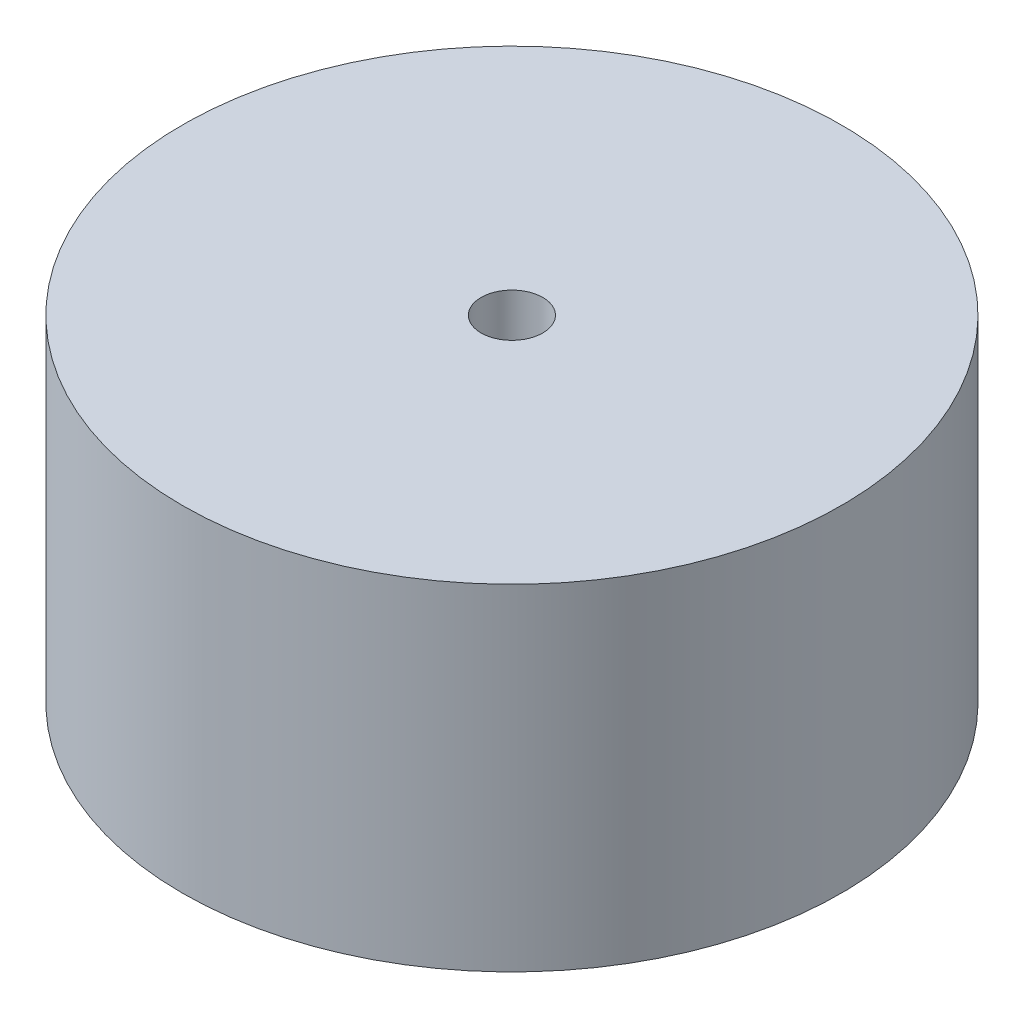
SolidWorks part; units mm, degrees
ref_plane "Front Plane" through (0, 0, 0) normal (0, 0, 1) x (1, 0, 0)
ref_plane "Top Plane" through (0, 0, 0) normal (0, 1, 0) x (1, 0, 0)
ref_plane "Right Plane" through (0, 0, 0) normal (1, 0, 0) x (0, 0, -1)
sketch "Sketch1" plane through (0, 0, 0) normal (0, 1, 0) x (1, 0, 0)
  circle A1 centre (0, 0) radius 17.375
extrude "Boss-Extrude1" add sketch "Sketch1" along normal blind 17.7
sketch "Sketch7" plane through (0, 0, 0) normal (0, -1, 0) x (1, 0, 0)
  circle A0 centre (0, 0) radius 13.545
extrude "Cut-Extrude4" cut sketch "Sketch7" against normal blind 8 contours A0
sketch "Sketch10" plane through (0, 8, 0) normal (0, -1, 0) x (1, 0, 0)
  circle A0 centre (0, 0) radius 3.485
extrude "Boss-Extrude3" add sketch "Sketch10" along normal blind 4 contours A0
sketch "Sketch11" plane through (0, 4, 0) normal (0, -1, 0) x (1, 0, 0)
  circle A3 centre (0, 0) radius 1.625
sketch "Sketch14" plane through (0, 8, 0) normal (0, -1, 0) x (1, 0, 0)
  point P10 (0, 0)
extrude "Cut-Extrude5" cut sketch "Sketch11" against normal up to surface (13.7 mm away) up to face at (0, 17.7, 17.375)
